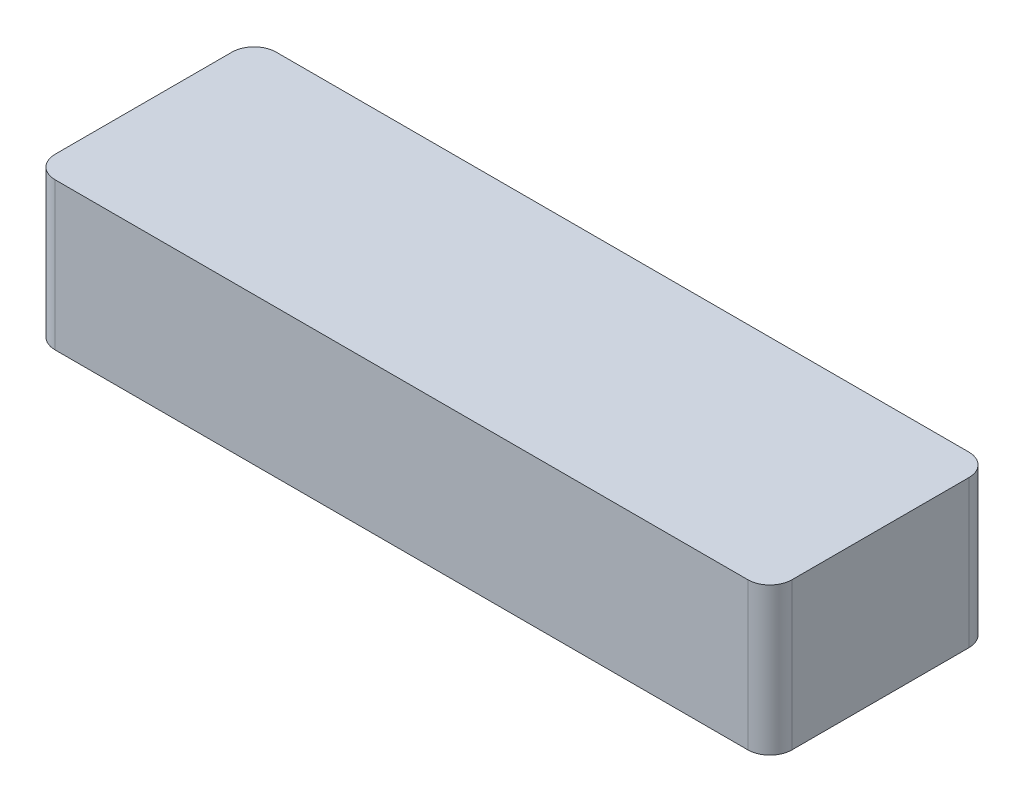
SolidWorks part; units mm, degrees
ref_plane "Front Plane" through (0, 0, 0) normal (0, 0, 1) x (1, 0, 0)
ref_plane "Top Plane" through (0, 0, 0) normal (0, 1, 0) x (1, 0, 0)
ref_plane "Right Plane" through (0, 0, 0) normal (1, 0, 0) x (0, 0, -1)
sketch "Sketch1" plane through (0, 0, 0) normal (0, 1, 0) x (1, 0, 0)
  line L1 (-235, -75) -> (235, -75)
  line L2 (-250, -60) -> (-250, 60)
  line L3 (-235, 75) -> (235, 75)
  line L4 (250, -60) -> (250, 60)
  line L5 (-250, -75) -> (250, 75) construction
  line L6 (-250, 75) -> (250, -75) construction
  arc A0 (-250, -60) -> (-235, -75) centre (-235, -60) ccw
  arc A1 (235, -75) -> (250, -60) centre (235, -60) ccw
  arc A2 (250, 60) -> (235, 75) centre (235, 60) ccw
  arc A3 (-235, 75) -> (-250, 60) centre (-235, 60) ccw
  point P0 (0, 0)
  dimension "D3" = 15
  dimension "D1" = 500
  dimension "D2" = 150
extrude "Boss-Extrude1" add sketch "Sketch1" along normal blind 100
shell "Shell1" thickness 5
